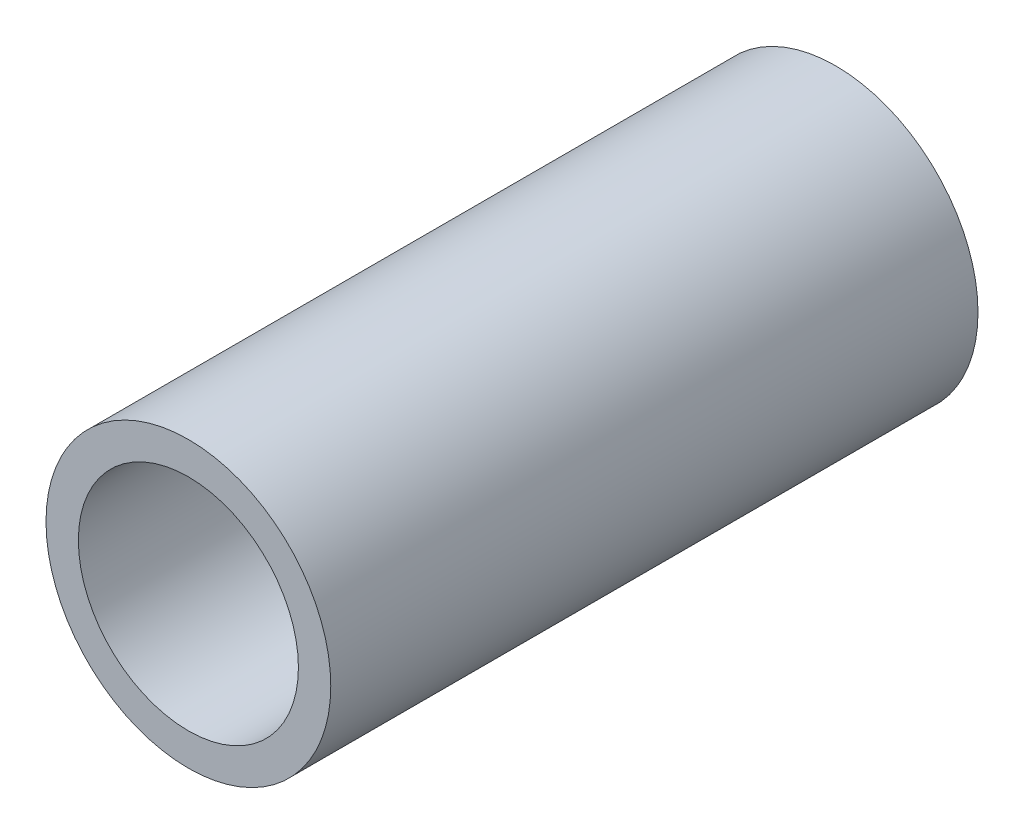
SolidWorks part; units mm, degrees
ref_plane "Alzado" through (0, 0, 0) normal (0, 0, 1) x (1, 0, 0)
ref_plane "Planta" through (0, 0, 0) normal (0, 1, 0) x (1, 0, 0)
ref_plane "Vista lateral" through (0, 0, 0) normal (1, 0, 0) x (0, 0, -1)
sketch "Croquis1" plane through (0, 0, 0) normal (0, 0, 1) x (1, 0, 0)
  circle A0 centre (0, 0) radius 2.2
  circle A1 centre (0, 0) radius 1.7
  dimension "D1" = 4.4
  dimension "D2" = 0.5
extrude "Saliente-Extruir1" add sketch "Croquis1" along normal blind 10
